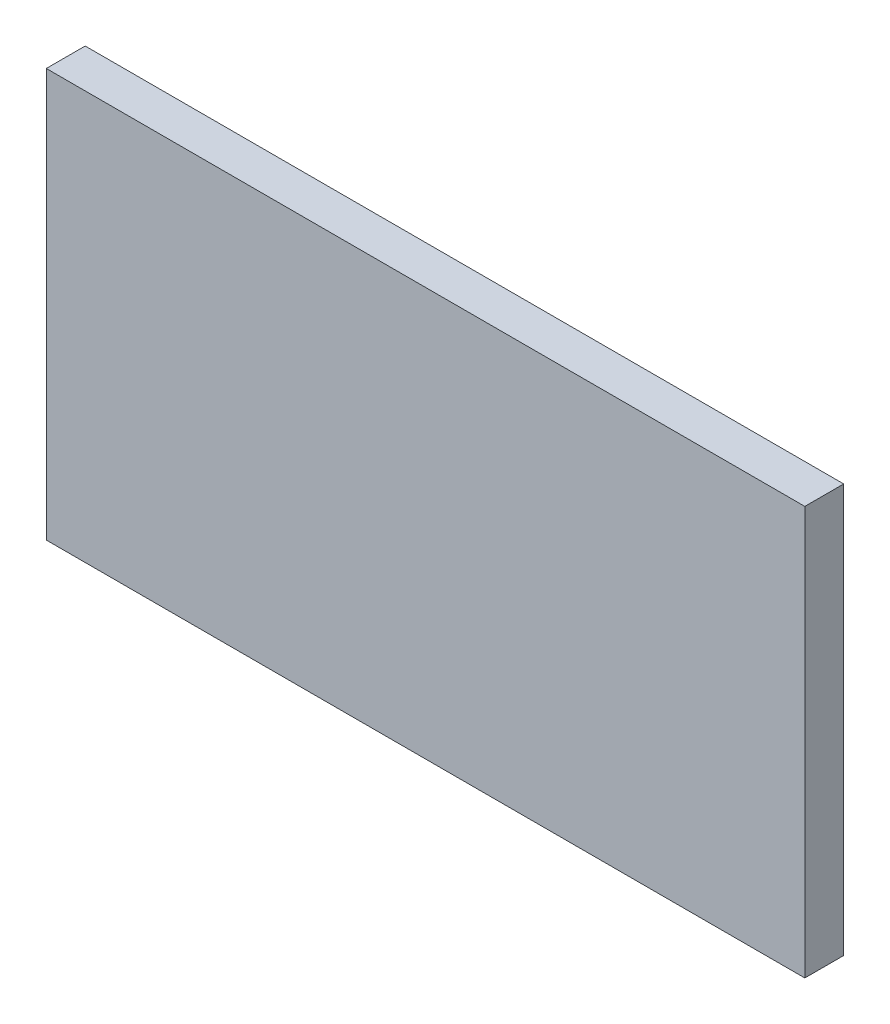
SolidWorks part; units mm, degrees
material "6061-T6 (SS)"
ref_plane "Front Plane" through (0, 0, 0) normal (0, 0, 1) x (1, 0, 0)
ref_plane "Top Plane" through (0, 0, 0) normal (0, 1, 0) x (1, 0, 0)
ref_plane "Right Plane" through (0, 0, 0) normal (1, 0, 0) x (0, 0, -1)
sketch "Sketch1" plane through (0, 0, 0) normal (0, 0, 1) x (1, 0, 0)
  line L11 (-50.8, 31.75) -> (73.025, 31.75)
  line L12 (-50.8, 31.75) -> (-50.8, -34.925)
  line L13 (-50.8, -34.925) -> (73.025, -34.925)
  line L14 (73.025, 31.75) -> (73.025, -34.925)
  circle A0 centre (-33.02, 0) radius 11.1125 construction
  circle A1 centre (33.02, 0) radius 11.1125 construction
  circle A2 centre (0, 0) radius 11.1125 construction
  circle A3 centre (-33.02, 0) radius 31.75 construction
  circle A4 centre (33.02, 0) radius 31.75 construction
  circle A5 centre (0, 0) radius 25.4 construction
  circle A6 centre (-33.02, 0) radius 7.62 construction
  circle A7 centre (33.02, 0) radius 7.62 construction
  point P27 (-50.8, -1.5875)
  dimension "D1" = 22.225
  dimension "D4" = 22.225
  dimension "D5" = 50.8
  dimension "D6" = 15.24
  dimension "D8" = 50.8
  dimension "D3" = 63.5
  dimension "D7" = 3.175
  dimension "D9" = 73.025
  dimension "D2" = 66.675
extrude "Boss-Extrude1" add sketch "Sketch1" along normal blind 6.35
